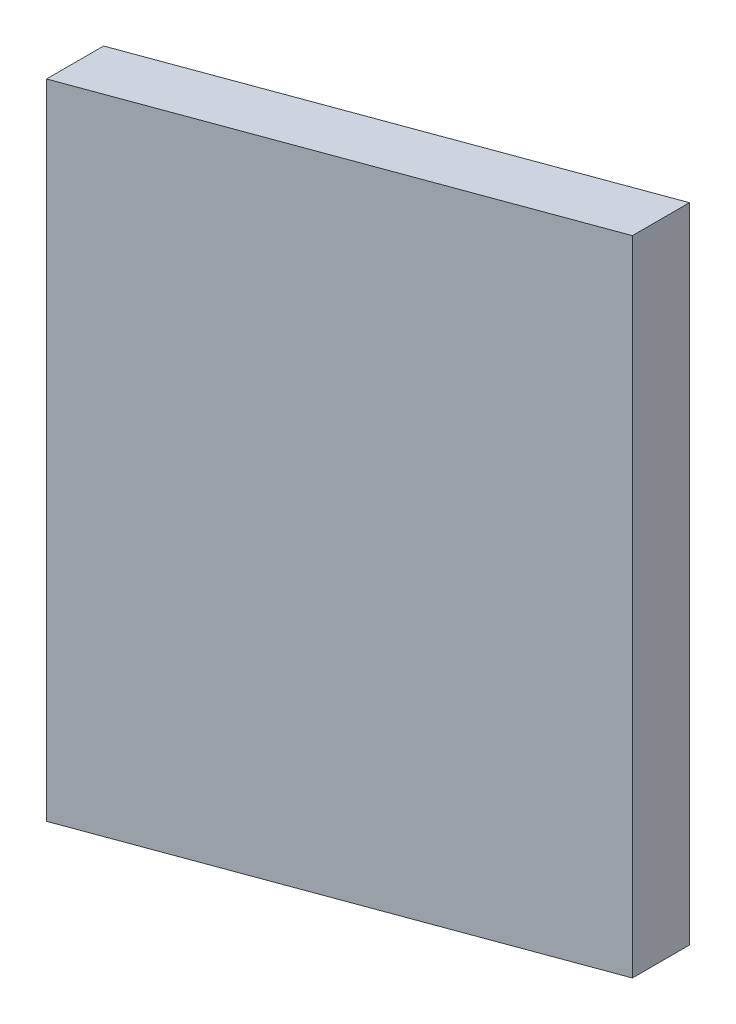
SolidWorks part; units mm, degrees
ref_plane "Front Plane" through (0, 0, 0) normal (0, 0, 1) x (1, 0, 0)
ref_plane "Top Plane" through (0, 0, 0) normal (0, 1, 0) x (1, 0, 0)
ref_plane "Right Plane" through (0, 0, 0) normal (1, 0, 0) x (0, 0, -1)
sketch "Sketch1" plane through (0, 0, 0) normal (0, 1, 0) x (1, 0, 0)
  line L0 (0, 0) -> (50.8, 18.6362)
  line L1 (50.8, 18.6362) -> (50.8, 25.4)
  line L2 (50.8, 25.4) -> (0, 6.7638)
  line L3 (0, 6.7638) -> (0, 0)
  point P3 (50.8, 25.4)
  point P6 (50.8, 18.9552)
  dimension "D1" = 50.8
  dimension "D2" = 25.4
  dimension "D3" = 6.35
extrude "Boss-Extrude1" add sketch "Sketch1" along normal blind 76.2
